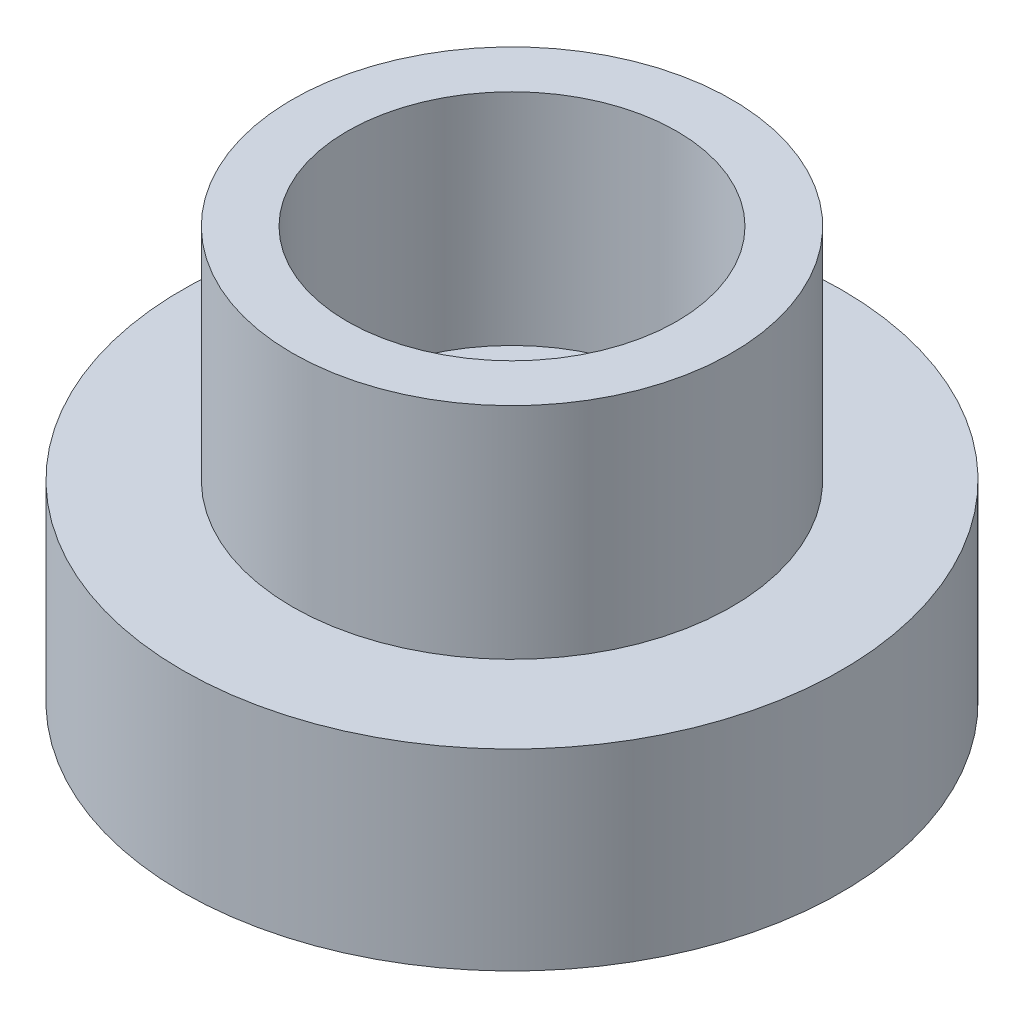
SolidWorks part; units mm, degrees
ref_plane "Front Plane" through (0, 0, 0) normal (0, 0, 1) x (1, 0, 0)
ref_plane "Top Plane" through (0, 0, 0) normal (0, 1, 0) x (1, 0, 0)
ref_plane "Right Plane" through (0, 0, 0) normal (1, 0, 0) x (0, 0, -1)
sketch "Sketch1" plane through (0, 0, 0) normal (0, 1, 0) x (1, 0, 0)
  circle A0 centre (0, 0) radius 38.1
  circle A2 centre (0, 0) radius 31.115
  dimension "D1" = 76.2
  dimension "D3" = 62.23
extrude "Boss-Extrude1" add sketch "Sketch1" along normal blind 19.05
sketch "Sketch2" plane through (0, 0, 0) normal (0, -1, 0) x (1, 0, 0)
  circle A0 centre (0, 0) radius 34.29 construction
  circle A1 centre (0, 34.29) radius 1.6497
  circle A2 centre (34.29, 0) radius 1.6497
  circle A3 centre (0, -34.29) radius 1.6497
  circle A4 centre (-34.29, 0) radius 1.6497
  dimension "D1" = 68.58
  dimension "D2" = 3.2995
  dimension "D3" = 4
extrude "Cut-Extrude1" cut sketch "Sketch2" against normal blind 12.7
cosmetic thread "Cosmetic Thread1" parameters "D2"=4.1656
cosmetic thread "Cosmetic Thread2" parameters "D2"=4.1656
cosmetic thread "Cosmetic Thread3" parameters "D2"=4.1656
cosmetic thread "Cosmetic Thread4" parameters "D2"=4.1656
sketch "Sketch3" plane through (0, 19.05, 0) normal (0, 1, 0) x (1, 0, 0)
  circle A0 centre (0, 0) radius 12.7
  circle A1 centre (0, 0) radius 38.1
  dimension "D1" = 25.4
extrude "Boss-Extrude2" add sketch "Sketch3" along normal blind 3.175
sketch "Sketch4" plane through (0, 22.225, 0) normal (0, 1, 0) x (1, 0, 0)
  circle A0 centre (0, 0) radius 19.05
  circle A1 centre (0, 0) radius 25.4
  dimension "D1" = 38.1
  dimension "D2" = 50.8
extrude "Boss-Extrude3" add sketch "Sketch4" along normal blind 25.4
